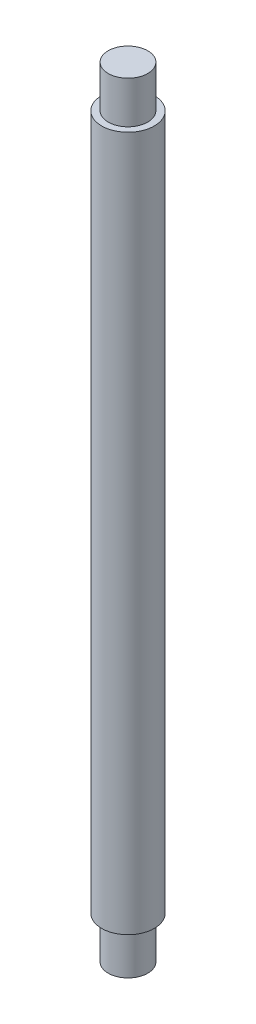
SolidWorks part; units mm, degrees
ref_plane "Alzado" through (0, 0, 0) normal (0, 0, 1) x (1, 0, 0)
ref_plane "Planta" through (0, 0, 0) normal (0, 1, 0) x (1, 0, 0)
ref_plane "Vista lateral" through (0, 0, 0) normal (1, 0, 0) x (0, 0, -1)
sketch "Croquis1" plane through (0, 0, 0) normal (0, 1, 0) x (1, 0, 0)
  circle A0 centre (0, 0) radius 2.5
  dimension "D1" = 5
extrude "Saliente-Extruir1" add sketch "Croquis1" along normal blind 66
sketch "Croquis2" plane through (0, 66, 0) normal (0, 1, 0) x (1, 0, 0)
  circle A0 centre (0, 0) radius 1.875
  dimension "D1" = 3.75
extrude "Saliente-Extruir2" add sketch "Croquis2" along normal blind 4
sketch "Croquis3" plane through (0, 0, 0) normal (0, -1, 0) x (1, 0, 0)
  circle A0 centre (0, 0) radius 1.875
  point P2 (0.2893, -0.3685)
  point P3 (0, 0)
  dimension "D1" = 3.75
extrude "Saliente-Extruir3" add sketch "Croquis3" along normal blind 4
